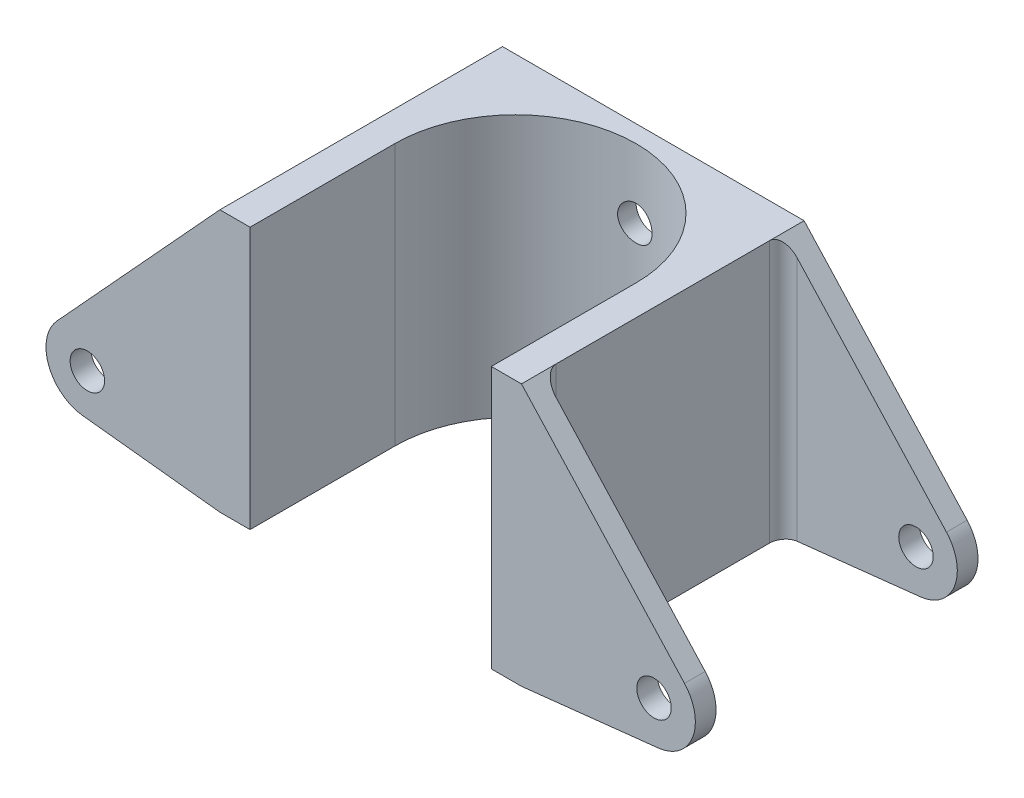
SolidWorks part; units mm, degrees
ref_plane "Front Plane" through (0, 0, 0) normal (0, 0, 1) x (1, 0, 0)
ref_plane "Top Plane" through (0, 0, 0) normal (0, 1, 0) x (1, 0, 0)
ref_plane "Right Plane" through (0, 0, 0) normal (1, 0, 0) x (0, 0, -1)
sketch "Sketch1" plane through (0, 0, 0) normal (0, 0, 1) x (1, 0, 0)
  line L0 (-21.875, 0) -> (-41.7558, 2.1805)
  line L1 (-21.875, 38) -> (21.875, 38)
  line L2 (-21.875, 38) -> (-21.875, 0) construction
  line L3 (-21.875, 0) -> (21.875, 0)
  line L4 (21.875, 38) -> (21.875, 0) construction
  line L5 (-45.5247, 12.199) -> (-21.875, 38)
  line L6 (0, -20.9) -> (0, 20.9) construction
  line L7 (21.875, 0) -> (41.7558, 2.1805)
  line L8 (45.5247, 12.199) -> (21.875, 38)
  arc A0 (-41.7558, 2.1805) -> (-45.5247, 12.199) centre (-41.1016, 8.1447) cw
  arc A1 (41.7558, 2.1805) -> (45.5247, 12.199) centre (41.1016, 8.1447) ccw
  dimension "D3" = 6
  dimension "D1" = 38
  dimension "D2" = 43.75
  dimension "D4" = 35
  dimension "D5" = 20
extrude "Boss-Extrude1" add sketch "Sketch1" along normal blind 41
sketch "Sketch3" plane through (0, 0, 0) normal (0, 1, 0) x (1, 0, 0)
  line L0 (21.875, -41) -> (21.875, 0) construction
  line L1 (21.875, -3) -> (47.1016, -3)
  line L2 (21.875, -3) -> (21.875, -38)
  line L3 (21.875, -38) -> (47.1016, -38)
  line L4 (47.1016, -3) -> (47.1016, -38)
  line L5 (47.1016, -41) -> (47.1016, 0) construction
  line L7 (-34.4883, -3) -> (-34.4883, 0) construction
  line L8 (0, -20.9) -> (0, 20.9) construction
  line L9 (-21.875, -3) -> (-21.875, -38)
  line L10 (-21.875, -38) -> (-47.1016, -38)
  line L11 (-47.1016, -3) -> (-47.1016, -38)
  line L12 (-21.875, -3) -> (-47.1016, -3)
  line L14 (-21.875, 0) -> (-45.5247, 0) construction
  line L15 (-34.4883, -38) -> (-34.4883, -41) construction
  line L16 (-21.875, -41) -> (-45.5247, -41) construction
  dimension "D1" = 35
extrude "Cut-Extrude2" cut sketch "Sketch3" against normal through all and the other way through all
sketch "Sketch4" plane through (0, 0, 0) normal (0, -1, 0) x (1, 0, 0)
  line L0 (-21.875, 41) -> (21.875, 41) construction
  line L2 (-17.5, 20) -> (-17.5, 41)
  line L3 (-17.5, 41) -> (17.5, 41)
  line L4 (17.5, 20) -> (17.5, 41)
  line L5 (-21.875, 0) -> (21.875, 0) construction
  arc A0 (-17.5, 20) -> (17.5, 20) centre (0, 20) ccw
  dimension "D1" = 17.5
  dimension "D2" = 20
extrude "Cut-Extrude3" cut sketch "Sketch4" against normal through all
sketch "Sketch5" plane through (0, 0, 0) normal (0, 0, -1) x (-1, 0, 0)
  line L0 (0, 28) -> (0, 10) construction
  line L1 (0, 0) -> (0, 38) construction
  line L2 (-21.875, 38) -> (21.875, 38) construction
  circle A0 centre (0, 28) radius 2.5
  circle A1 centre (0, 10) radius 2.5
  point P10 (0, 19)
  point P11 (0, 19)
  dimension "D1" = 5
  dimension "D2" = 10
extrude "Cut-Extrude4" cut sketch "Sketch5" against normal through all
sketch "Sketch6" plane through (0, 0, 41) normal (0, 0, 1) x (1, 0, 0)
  circle A0 centre (-41.1016, 8.1447) radius 2.5
  arc A1 (-45.5247, 12.199) -> (-41.7558, 2.1805) centre (-41.1016, 8.1447) ccw construction
  dimension "D1" = 5
extrude "Cut-Extrude5" cut sketch "Sketch6" against normal through all contours A0
mirror "Mirror1" about plane through (0, 0, 0) normal (1, 0, 0) of "Cut-Extrude5"
fillet "Fillet1" radius 2 4 edges at (21.875, 19, 38) (21.875, 19, 3) (-21.875, 19, 38) (-21.875, 19, 3)
equation "\"tubeOutDiameter\" = 35mm"
equation "\"wheelShaftDiameter\"= 12mm"
equation "\"wheelThickness\"= 135mm"
equation "\"BearingDiameter\"= 20mm"
equation "\"BearingThickness\"= 10mm"
equation "\"frontShaftDiameter\"= 20mm"
equation "\"D2@Sketch1\"=\"tubeOutDiameter\"*1.25"
equation "\"D1@Sketch3\"=\"tubeOutDiameter\""
equation "\"D1@Sketch4\"=\"tubeOutDiameter\"/2"
